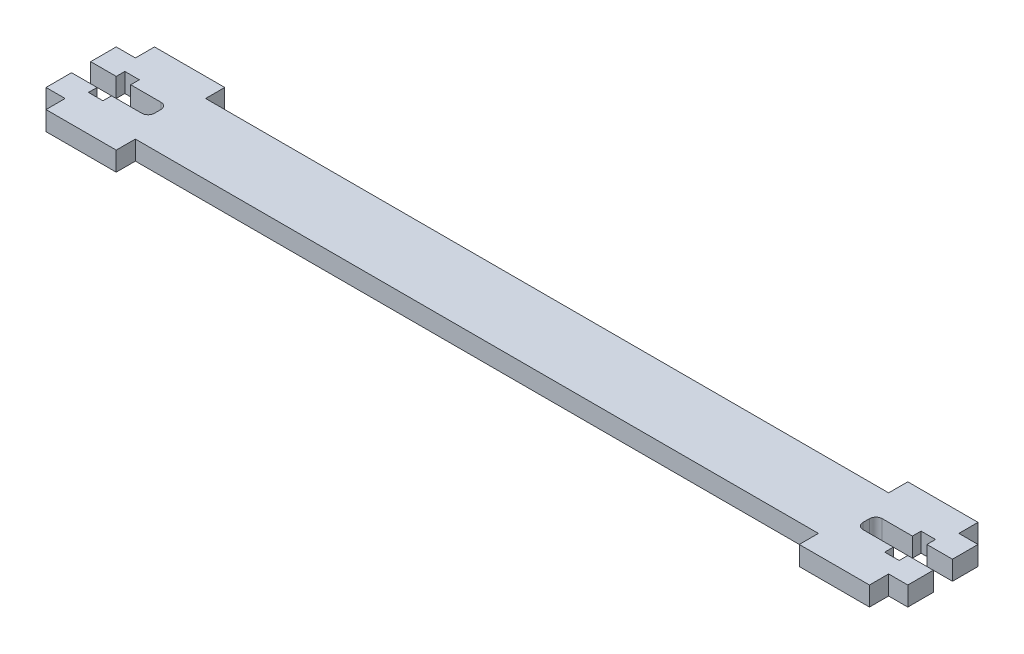
SolidWorks part; units mm, degrees
ref_plane "Plano frontal" through (0, 0, 0) normal (0, 0, 1) x (1, 0, 0)
ref_plane "Plano superior" through (0, 0, 0) normal (0, 1, 0) x (1, 0, 0)
ref_plane "Plano direito" through (0, 0, 0) normal (1, 0, 0) x (0, 0, -1)
sketch "Sketch1" plane through (0, 0, 0) normal (0, 1, 0) x (1, 0, 0)
  line L1 (-53.5, 5.5) -> (53.5, 5.5)
  line L2 (-53.5, 5.5) -> (-53.5, -5.5)
  line L3 (-53.5, -5.5) -> (53.5, -5.5)
  line L4 (53.5, 5.5) -> (53.5, -5.5)
  point P4 (-53.5, 0)
  point P6 (0, 5.5)
  dimension "D1" = 107
  dimension "D2" = 11
extrude "Boss-Extrude1" add sketch "Sketch1" along normal mid plane 3
sketch "Sketch3" plane through (0, 0, 0) normal (0, 1, 0) x (1, 0, 0)
  line L0 (-53.5, 5.5) -> (-53.5, -5.5) construction
  line L1 (-64.5, 8.5) -> (-53.5, 8.5)
  line L2 (-64.5, 8.5) -> (-64.5, -8.5)
  line L3 (-64.5, -8.5) -> (-53.5, -8.5)
  line L4 (-53.5, 8.5) -> (-53.5, -8.5)
  line L5 (53.5, 5.5) -> (-53.5, 5.5) construction
  line L6 (0, -1.65) -> (0, 1.65) construction
  line L7 (53.5, 8.5) -> (53.5, -8.5)
  line L8 (64.5, -8.5) -> (53.5, -8.5)
  line L9 (64.5, 8.5) -> (64.5, -8.5)
  line L10 (64.5, 8.5) -> (53.5, 8.5)
  point P8 (-53.5, 0)
  dimension "D1" = 11
  dimension "D2" = 3
extrude "Boss-Extrude2" add sketch "Sketch3" along normal mid plane 3
sketch "Sketch4" plane through (0, 0, 0) normal (0, 1, 0) x (1, 0, 0)
  line L1 (-64.5, 5.5) -> (-67.5, 5.5)
  line L2 (-64.5, 5.5) -> (-64.5, -5.5)
  line L3 (-64.5, -5.5) -> (-67.5, -5.5)
  line L4 (-67.5, 5.5) -> (-67.5, -5.5)
  line L7 (-64.5, 8.5) -> (-64.5, -8.5) construction
  line L8 (53.5, 5.5) -> (-53.5, 5.5) construction
  line L9 (-53.5, -5.5) -> (53.5, -5.5) construction
  line L10 (0, -1.65) -> (0, 1.65) construction
  line L11 (67.5, 5.5) -> (67.5, -5.5)
  line L12 (64.5, -5.5) -> (67.5, -5.5)
  line L13 (64.5, 5.5) -> (64.5, -5.5)
  line L14 (64.5, 5.5) -> (67.5, 5.5)
  dimension "D1" = 3
extrude "Boss-Extrude3" add sketch "Sketch4" along normal mid plane 3
sketch "Sketch2" plane through (0, 0, 0) normal (0, 1, 0) x (1, 0, 0)
  line L1 (-67.5, 1.5) -> (-63.5, 1.5)
  line L2 (-67.5, 1.5) -> (-67.5, -1.5)
  line L3 (-67.5, -1.5) -> (-63.5, -1.5)
  line L4 (-55.5, 0.5) -> (-55.5, -0.5)
  line L5 (-61.23, 1.5) -> (-56.5, 1.5)
  line L6 (-63.5, 2.85) -> (-61.23, 2.85)
  line L7 (-63.5, 2.85) -> (-63.5, 1.5)
  line L8 (-63.5, -2.85) -> (-61.23, -2.85)
  line L9 (-61.23, 2.85) -> (-61.23, 1.5)
  line L10 (-63.5, -1.5) -> (-63.5, -2.85)
  line L11 (-61.23, -1.5) -> (-61.23, -2.85)
  line L12 (-61.23, -1.5) -> (-56.5, -1.5)
  line L13 (0, -1.65) -> (0, 1.65) construction
  line L14 (61.23, -1.5) -> (56.5, -1.5)
  line L15 (61.23, -1.5) -> (61.23, -2.85)
  line L16 (63.5, -1.5) -> (63.5, -2.85)
  line L17 (61.23, 2.85) -> (61.23, 1.5)
  line L18 (63.5, -2.85) -> (61.23, -2.85)
  line L19 (63.5, 2.85) -> (63.5, 1.5)
  line L20 (63.5, 2.85) -> (61.23, 2.85)
  line L21 (61.23, 1.5) -> (56.5, 1.5)
  line L22 (55.5, 0.5) -> (55.5, -0.5)
  line L23 (67.5, -1.5) -> (63.5, -1.5)
  line L24 (67.5, 1.5) -> (67.5, -1.5)
  line L25 (67.5, 1.5) -> (63.5, 1.5)
  line L28 (-67.5, 5.5) -> (-67.5, -5.5) construction
  arc A0 (-56.5, -1.5) -> (-55.5, -0.5) centre (-56.5, -0.5) ccw
  arc A1 (-56.5, 1.5) -> (-55.5, 0.5) centre (-56.5, 0.5) cw
  arc A2 (56.5, 1.5) -> (55.5, 0.5) centre (56.5, 0.5) ccw
  arc A3 (56.5, -1.5) -> (55.5, -0.5) centre (56.5, -0.5) cw
  point P6 (-67.5, 0)
  point P20 (-55.5, 1.5)
  point P39 (55.5, 1.5)
  dimension "D7" = 1
  dimension "D1" = 3
  dimension "D2" = 12
  dimension "D3" = 1.35
  dimension "D4" = 1.35
  dimension "D5" = 4
  dimension "D6" = 2.27
extrude "Cut-Extrude1" cut sketch "Sketch2" against normal through all both and the other way through all
